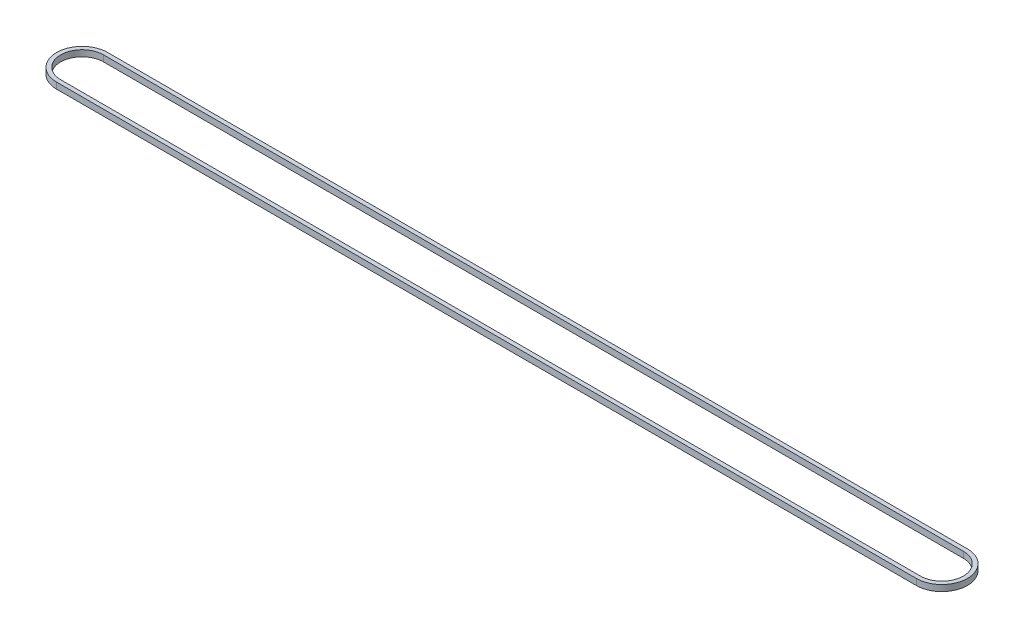
SolidWorks part; units mm, degrees
ref_plane "Front Plane" through (0, 0, 0) normal (0, 0, 1) x (1, 0, 0)
ref_plane "Top Plane" through (0, 0, 0) normal (0, 1, 0) x (1, 0, 0)
ref_plane "Right Plane" through (0, 0, 0) normal (1, 0, 0) x (0, 0, -1)
sketch "Sketch1" plane through (0, 0, 0) normal (0, 1, 0) x (1, 0, 0)
  line L0 (-32.6689, 12.5) -> (387.3311, 12.5)
  line L1 (-32.6689, -12.5) -> (387.3311, -12.5)
  line L2 (-32.6689, 10.5) -> (387.3311, 10.5)
  line L3 (-32.6689, -10.5) -> (387.3311, -10.5)
  arc A0 (-32.6689, 12.5) -> (-32.6689, -12.5) centre (-32.6689, 0) ccw
  arc A1 (387.3311, -12.5) -> (387.3311, 12.5) centre (387.3311, 0) ccw
  arc A2 (387.3311, -10.5) -> (387.3311, 10.5) centre (387.3311, 0) ccw
  arc A3 (-32.6689, 10.5) -> (-32.6689, -10.5) centre (-32.6689, 0) ccw
  dimension "D1" = 25
  dimension "D2" = 2
  dimension "D3" = 420
extrude "Boss-Extrude1" add sketch "Sketch1" along normal blind 3
